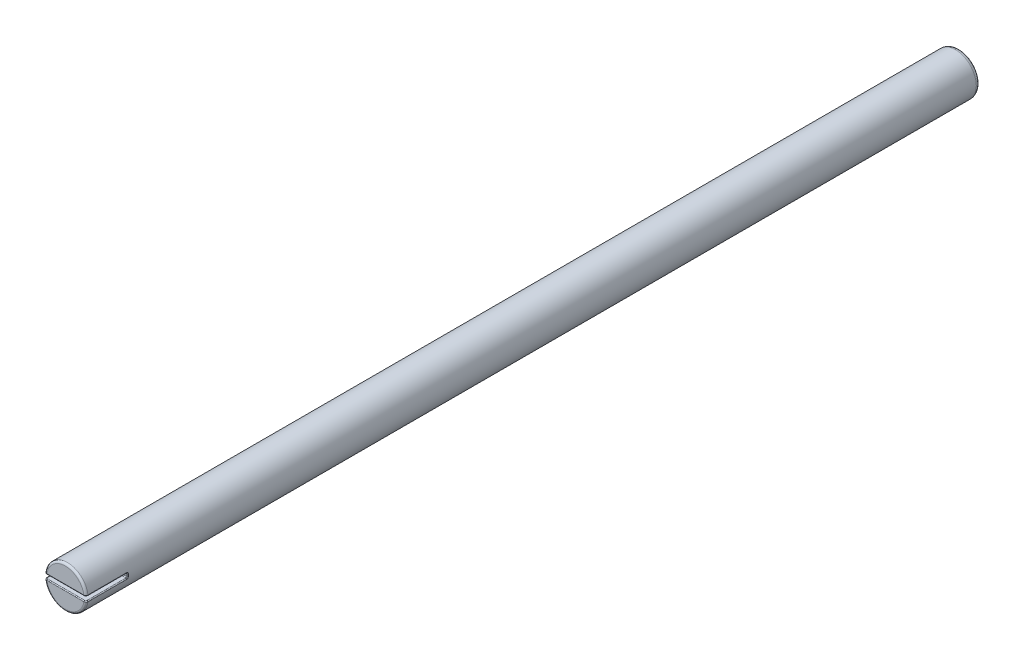
SolidWorks part; units mm, degrees
ref_plane "Front Plane" through (0, 0, 0) normal (0, 0, 1) x (1, 0, 0)
ref_plane "Top Plane" through (0, 0, 0) normal (0, 1, 0) x (1, 0, 0)
ref_plane "Right Plane" through (0, 0, 0) normal (1, 0, 0) x (0, 0, -1)
sketch "Sketch1" plane through (0, 0, 0) normal (0, 0, 1) x (1, 0, 0)
  circle A0 centre (0, 0) radius 0.5
  dimension "D1" = 1
extrude "Boss-Extrude1" add sketch "Sketch1" along normal blind 21.5
sketch "Sketch2" plane through (0, 0, 21.5) normal (0, 0, 1) x (1, 0, 0)
  line L0 (0.55, 0) -> (-0.55, 0) construction
  line L1 (-0.6613, 0.05) -> (0.9478, 0.05)
  line L2 (-0.6613, 0.05) -> (-0.6613, -0.05)
  line L3 (-0.6613, -0.05) -> (0.9478, -0.05)
  line L4 (0.9478, 0.05) -> (0.9478, -0.05)
  dimension "D1" = 0.05
  dimension "D2" = 0.05
extrude "Cut-Extrude1" cut sketch "Sketch2" against normal blind 1
fillet "Fillet1" radius 0.1 1 edges at (0.5, 0, 0)
fillet "Fillet2" radius 0.05 2 edges at (0, -0.5, 21.5) (0, 0.5, 21.5)
fillet "Fillet3" radius 0.02 14 edges at (0, 0.05, 21.5) (0, -0.05, 21.5) (-0.4788, 0.05, 21.4889) (0.4866, 0.05, 21.4811) (0.4788, -0.05, 21.4889) (-0.4866, -0.05, 21.4811) (-0.4975, 0.05, 20.975) (0.4975, 0.05, 20.975) (0.4975, -0.05, 20.975) (-0.4975, -0.05, 20.975) (0, 0.05, 20.5) (-0.5, 0, 20.5) (0.5, 0, 20.5) (0, -0.05, 20.5)
